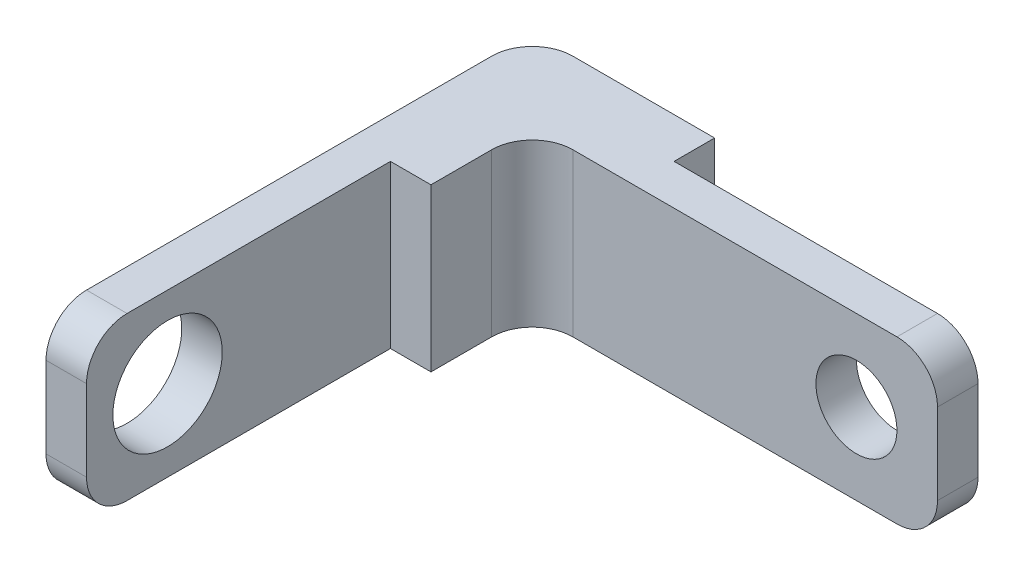
SolidWorks part; units mm, degrees
ref_plane "Ön Düzlem" through (0, 0, 0) normal (0, 0, 1) x (1, 0, 0)
ref_plane "Üst Düzlem" through (0, 0, 0) normal (0, 1, 0) x (1, 0, 0)
ref_plane "Sağ Düzlem" through (0, 0, 0) normal (1, 0, 0) x (0, 0, -1)
sketch "Sketch2" plane through (0, 0, 0) normal (0, 0, 1) x (1, 0, 0)
  line L1 (-60, 20) -> (60, 20)
  line L2 (-60, 20) -> (-60, -20)
  line L3 (-60, -20) -> (60, -20)
  line L4 (60, 20) -> (60, -20)
  line L5 (-60, 20) -> (60, -20) construction
  line L6 (-60, -20) -> (60, 20) construction
  point P0 (0, 0)
  dimension "D1" = 120
  dimension "D2" = 40
extrude "Boss-Extrude1" add sketch "Sketch2" along normal blind 20
sketch "Sketch3" plane through (0, 0, 20) normal (0, 0, 1) x (1, 0, 0)
  line L0 (-60, -20) -> (60, -20) construction
  line L1 (-60, 20) -> (-40, 20)
  line L2 (-60, 20) -> (-60, -20)
  line L3 (-60, -20) -> (-40, -20)
  line L4 (-40, 20) -> (-40, -20)
  dimension "D1" = 20
extrude "Boss-Extrude2" add sketch "Sketch3" along normal blind 100
sketch "Sketch4" plane through (0, 0, 0) normal (0, 0, -1) x (-1, 0, 0)
  line L0 (60, -20) -> (-60, -20) construction
  line L1 (-60, 20) -> (15, 20)
  line L2 (-60, 20) -> (-60, -20)
  line L3 (-60, -20) -> (15, -20)
  line L4 (15, 20) -> (15, -20)
  dimension "D1" = 75
extrude "Cut-Extrude1" cut sketch "Sketch4" against normal blind 10
sketch "Sketch5" plane through (-40, 0, 0) normal (1, 0, 0) x (0, 0, -1)
  line L0 (-120, -20) -> (-20, -20) construction
  line L1 (-120, 20) -> (-45, 20)
  line L2 (-120, 20) -> (-120, -20)
  line L3 (-120, -20) -> (-45, -20)
  line L4 (-45, 20) -> (-45, -20)
  dimension "D1" = 75
extrude "Cut-Extrude2" cut sketch "Sketch5" against normal blind 10
sketch "Sketch6" plane through (-50, 0, 0) normal (1, 0, 0) x (0, 0, -1)
  line L0 (-120, 20) -> (-120, -20) construction
  circle A0 centre (-100, 0) radius 13.5
  dimension "D1" = 20
extrude "Cut-Extrude3" cut sketch "Sketch6" against normal up to next
fillet "Fillet2" radius 10 5 edges at (60, 20, 15) (60, -20, 15) (-55, -20, 120) (-55, 20, 120) (-60, 0, 0)
sketch "Sketch7" plane through (0, 0, 20) normal (0, 0, 1) x (1, 0, 0)
  line L0 (60, -10) -> (60, 10) construction
  circle A0 centre (40, 0) radius 10
  dimension "D1" = 20
extrude "Cut-Extrude4" cut sketch "Sketch7" against normal blind 10
fillet "Fillet3" radius 10 1 edges
